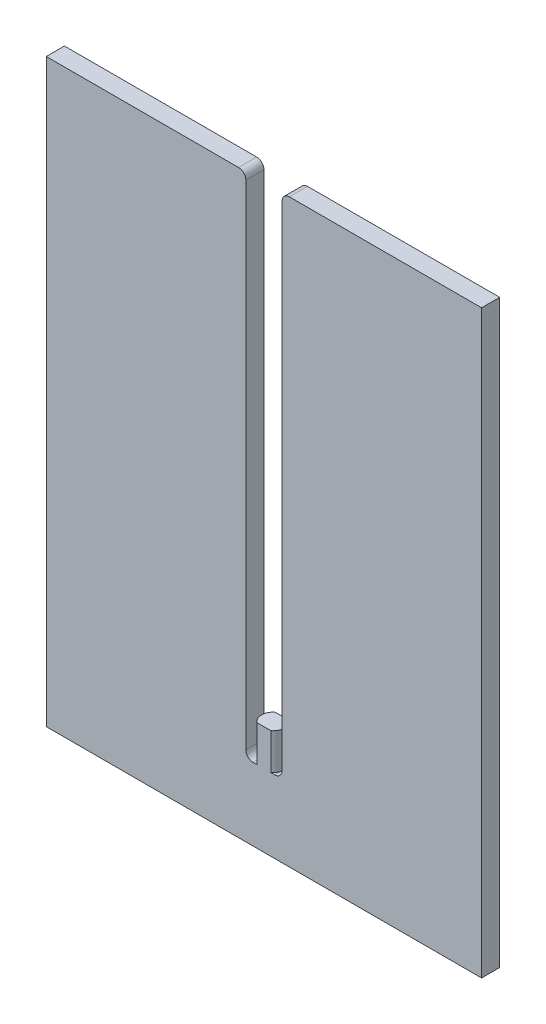
SolidWorks part; units mm, degrees
ref_plane "Front Plane" through (0, 0, 0) normal (0, 0, 1) x (1, 0, 0)
ref_plane "Top Plane" through (0, 0, 0) normal (0, 1, 0) x (1, 0, 0)
ref_plane "Right Plane" through (0, 0, 0) normal (1, 0, 0) x (0, 0, -1)
sketch "Sketch1" plane through (0, 0, 0) normal (0, 0, 1) x (1, 0, 0)
  line L0 (-2.5, 40) -> (-2.5, -30)
  line L1 (-30, 40) -> (-2.5, 40)
  line L2 (-30, 40) -> (-30, -40)
  line L3 (-30, -40) -> (30, -40)
  line L4 (30, 40) -> (30, -40)
  line L5 (-30, 40) -> (30, -40) construction
  line L6 (-30, -40) -> (30, 40) construction
  line L7 (0, 0) -> (0, 62.4551) construction
  line L8 (-2.5, -30) -> (2.5, -30)
  line L9 (2.5, 40) -> (2.5, -30)
  line L10 (2.5, 40) -> (30, 40)
  point P0 (0, 0)
  point P12 (0, -30)
  dimension "D1" = 60
  dimension "D2" = 80
  dimension "D3" = 5
  dimension "D4" = 70
extrude "Boss-Extrude1" add sketch "Sketch1" along normal blind 2.5
fillet "Fillet1" radius 1 4 edges at (-2.5, -30, 1.25) (2.5, -30, 1.25) (-2.5, 40, 1.25) (2.5, 40, 1.25)
sketch "Sketch2" plane through (0, -30, 0) normal (0, 1, 0) x (1, 0, 0)
  line L0 (1.5, -1.25) -> (-1.5, -1.25) construction
  line L1 (1.5, -2.5) -> (1.5, 0) construction
  line L2 (-1.5, 0) -> (-1.5, -2.5) construction
  line L3 (0, 0) -> (0, -2.5) construction
  line L4 (1.5, 0) -> (-1.5, 0) construction
  line L5 (1.5, -2.5) -> (-1.5, -2.5) construction
  line L6 (-0.9579, 0) -> (0.9579, 0)
  line L7 (0.9579, -2.5) -> (-0.9579, -2.5)
  arc A0 (0.9579, -2.5) -> (0.9579, 0) centre (0, -1.25) ccw
  arc A1 (-0.9579, 0) -> (-0.9579, -2.5) centre (0, -1.25) ccw
  dimension "D1" = 3.1496
extrude "Boss-Extrude2" add sketch "Sketch2" along normal blind 5
